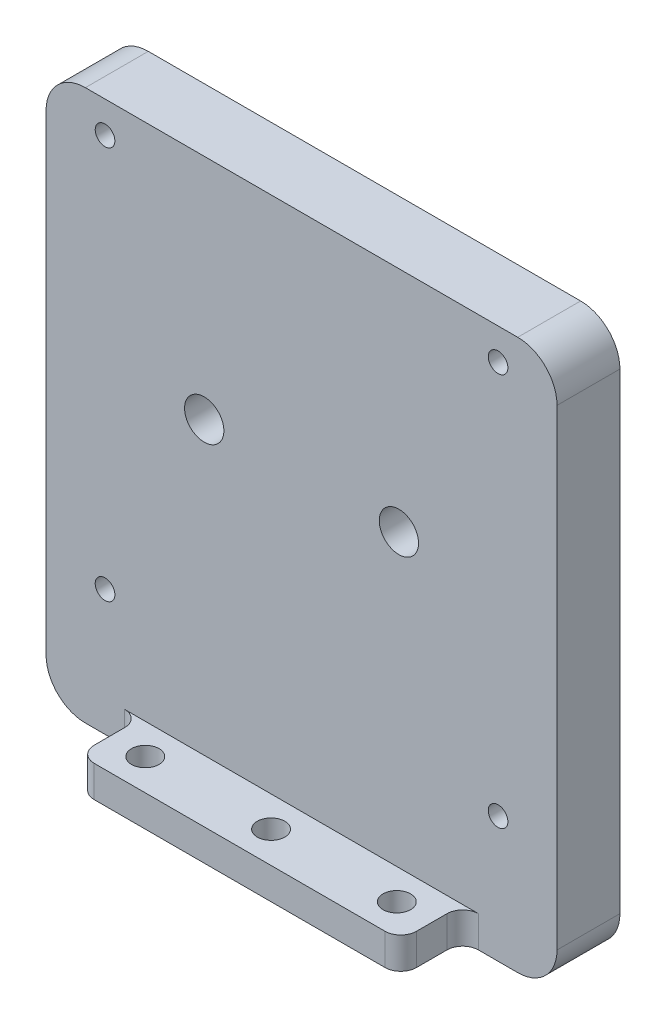
SolidWorks part; units mm, degrees
ref_plane "Front Plane" through (0, 0, 0) normal (0, 0, 1) x (1, 0, 0)
ref_plane "Top Plane" through (0, 0, 0) normal (0, 1, 0) x (1, 0, 0)
ref_plane "Right Plane" through (0, 0, 0) normal (1, 0, 0) x (0, 0, -1)
sketch "Sketch1" plane through (0, 0, 0) normal (0, 0, 1) x (1, 0, 0)
  line L0 (0, 4) -> (0, 0) construction
  line L1 (-32.5, 35) -> (32.5, 35)
  line L2 (-32.5, 35) -> (-32.5, -35)
  line L3 (-32.5, -35) -> (32.5, -35)
  line L4 (32.5, 35) -> (32.5, -35)
  line L5 (-32.5, 35) -> (32.5, -35) construction
  line L6 (-32.5, -35) -> (32.5, 35) construction
  line L7 (25, -21) -> (-25, -21) construction
  line L8 (25, -21) -> (25, 29) construction
  line L9 (25, 29) -> (-25, 29) construction
  line L10 (-25, -21) -> (-25, 29) construction
  line L11 (25, -21) -> (-25, 29) construction
  line L12 (25, 29) -> (-25, -21) construction
  point P0 (0, 0)
  point P6 (0, 4)
  dimension "D1" = 70
  dimension "D2" = 65
  dimension "D4" = 50
  dimension "D5" = 6
extrude "Boss-Extrude1" add sketch "Sketch1" along normal blind 8
fillet "Fillet1" radius 5 4 edges at (32.5, -35, 4) (-32.5, -35, 4) (32.5, 35, 4) (-32.5, 35, 4)
sketch "Sketch2" plane through (0, 0, 8) normal (0, 0, 1) x (1, 0, 0)
  line L0 (-27.5, -35) -> (27.5, -35) construction
  line L1 (-20.5, -35) -> (20.5, -35)
  line L2 (-20.5, -35) -> (-20.5, -31)
  line L3 (-20.5, -31) -> (20.5, -31)
  line L4 (20.5, -35) -> (20.5, -31)
  line L5 (0, 0) -> (0, -31) construction
  dimension "D1" = 41
  dimension "D2" = 4
extrude "Boss-Extrude2" add sketch "Sketch2" along normal blind 7.8799
fillet "Fillet2" radius 2 4 edges at (20.5, -33, 8) (20.5, -33, 15.8799) (-20.5, -33, 15.8799) (-20.5, -33, 8)
sketch "草图1" plane through (0, -35, 0) normal (0, -1, 0) x (1, 0, 0)
  line L0 (-16, 11.8799) -> (0, 11.8799) construction
  line L1 (0, 11.8799) -> (16, 11.8799) construction
  line L2 (-18.5, 15.8799) -> (18.5, 15.8799) construction
  circle A0 centre (-16, 11.8799) radius 1.75
  circle A1 centre (0, 11.8799) radius 1.75
  circle A2 centre (16, 11.8799) radius 1.75
  dimension "D2" = 3.5
  dimension "D1" = 16
  dimension "D3" = 4
extrude "切除-拉伸1" cut sketch "草图1" against normal through all
sketch "草图2" plane through (0, 0, 0) normal (0, 0, -1) x (-1, 0, 0)
  line L0 (-25, 31) -> (25, -19) construction
  line L1 (-25, 31) -> (25, 31) construction
  line L2 (-25, 31) -> (-25, -19) construction
  line L3 (-25, -19) -> (25, -19) construction
  line L4 (25, 31) -> (25, -19) construction
  line L5 (-27.5, 35) -> (27.5, 35) construction
  point P4 (0, 6)
  point P8 (0, 35)
  dimension "D1" = 50
  dimension "D2" = 50
  dimension "D3" = 4
hole_wizard "M3 螺纹孔1" positions "3D草图1" profile "草图3" tap size "M3" standard "ISO"
sketch3d "3D草图1"
  point P0 (25, -19, 0)
  point P3 (25, 31, 0)
  point P6 (-25, 31, 0)
  point P9 (-25, -19, 0)
sketch "草图3" plane through (25, -19, 0) normal (1, 0, 0) x (0, 1, 0)
  line L0 (0, 0) -> (0, 10.7511)
  line L1 (0, 10.7511) -> (1.25, 10)
  line L2 (1.25, 10) -> (1.25, 0)
  line L5 (1.25, 0) -> (0, 0)
  line L10 (0, 10.7511) -> (-1.25, 10) construction
  line L11 (0, -6.35) -> (0, 107.95) construction
  dimension "螺纹孔钻头直径" = 2.5
  dimension "螺纹孔钻头深度" = 10
  dimension "导头角度" = 118
cosmetic thread "孔螺蚊线1" parameters "D1"=6, "D2"=3
cosmetic thread "孔螺蚊线2" parameters "D1"=6, "D2"=3
cosmetic thread "孔螺蚊线3" parameters "D1"=6, "D2"=3
cosmetic thread "孔螺蚊线4" parameters "D1"=6, "D2"=3
ref_plane "基准面1" through (0, 0, -30.31) normal (0, 0, -1) x (-1, 0, 0)
sketch "草图11" plane through (0, 0, -30.31) normal (0, 0, -1) x (-1, 0, 0)
  line L0 (-32.5, 34.15) -> (-32.5, 36.65) construction
  line L1 (32.5, -35) -> (-32.5, -35)
  line L2 (32.5, -35) -> (32.5, 35.4)
  line L3 (32.5, 35.4) -> (-32.5, 35.4)
  line L4 (-32.5, -35) -> (-32.5, 35.4)
extrude "凸台-拉伸1" add sketch "草图11" against normal blind 2.9 separate body
fillet "圆角2" radius 5 1 edges at (-32.5, 35.4, -28.86)
fillet "圆角3" radius 5 1 edges at (-32.5, -35, -28.86)
fillet "圆角4" radius 5 1 edges at (32.5, -35, -28.86)
fillet "圆角5" radius 5 1 edges at (32.5, 35.4, -28.86)
sketch "草图15" plane through (0, 0, -30.31) normal (0, 0, -1) x (-1, 0, 0)
  circle A0 centre (-25, -19) radius 1.7
  circle A1 centre (-25, 31) radius 1.7
  circle A2 centre (25, -19) radius 1.7
  circle A3 centre (25, 31) radius 1.7
hole_wizard "M3 螺纹孔2" positions "草图23" profile "草图24" tap size "M3" standard "ISO" end condition up to next
sketch "草图23" plane through (0, 0, -30.31) normal (0, 0, -1) x (-1, 0, 0)
  point P0 (-25, 31)
  point P3 (25, 31)
  point P6 (-25, -19)
  point P9 (25, -19)
cosmetic thread "孔螺蚊线5" parameters "D2"=3
cosmetic thread "孔螺蚊线6" parameters "D2"=3
cosmetic thread "孔螺蚊线7" parameters "D2"=3
cosmetic thread "孔螺蚊线8" parameters "D2"=3
sketch "草图24" plane through (25, 31, -30.31) normal (1, 0, 0) x (0, 1, 0)
  line L0 (0, 0) -> (0, 2.901)
  line L1 (0, 2.901) -> (1.25, 2.901)
  line L2 (1.25, 2.901) -> (1.25, 0)
  line L5 (1.25, 0) -> (0, 0)
  line L11 (0, -6.35) -> (0, 107.95) construction
  dimension "通孔螺纹孔钻头直径" = 2.5
  dimension "通孔螺纹孔钻头深度" = 2.901
hole_wizard "M4 六角凹头螺钉的柱形沉头孔2" positions "草图26" profile "草图27" counterbore size "M4" standard "ISO" end condition up to next
sketch "草图26" plane through (0, 0, -30.31) normal (0, 0, -1) x (-1, 0, 0)
  point P0 (-9.4177, -9.82)
  point P3 (7.7273, -9.82)
  point P6 (7.7272, 19.876)
  point P9 (-9.4178, 19.876)
sketch "草图27" plane through (9.4177, -9.82, -30.31) normal (1, 0, 0) x (0, 1, 0)
  line L0 (0, 0) -> (0, 38.31)
  line L1 (0, 38.31) -> (2.25, 38.31)
  line L3 (2.25, 38.31) -> (2.25, 1.5)
  line L4 (2.25, 1.5) -> (4, 1.5)
  line L5 (4, 1.5) -> (4, 0)
  line L7 (4, 0) -> (0, 0)
  line L11 (0, -6.35) -> (0, 107.95) construction
  dimension "通孔孔直径" = 4.5
  dimension "通孔孔深度" = 38.31
  dimension "柱形沉头孔直径" = 8
  dimension "柱形沉头孔深度" = 1.5
sketch "草图28" plane through (32.5, 0, 0) normal (1, 0, 0) x (0, 0, -1)
  line L1 (21.2827, 40.5552) -> (37.6286, 40.5552)
  line L2 (21.2827, 40.5552) -> (21.2827, -44.2702)
  line L3 (21.2827, -44.2702) -> (37.6286, -44.2702)
  line L4 (37.6286, 40.5552) -> (37.6286, -44.2702)
extrude "切除-拉伸4" cut sketch "草图28" against normal through all
sketch "草图29" plane through (0, 0, 0) normal (0, 0, -1) x (-1, 0, 0)
  line L0 (-12.3825, 6) -> (12.3825, 6) construction
  line L1 (25, 31) -> (25, -19) construction
  line L2 (-25, -19) -> (25, -19) construction
  point P2 (0, 6)
  point P5 (25, 6)
  point P6 (-8.3163, 6)
  point P9 (0, -19)
  dimension "D1" = 24.765
hole_wizard "M6 螺纹孔1" positions "3D草图2" profile "草图30" tap size "M6" standard "ISO" end condition through all
sketch3d "3D草图2"
  point P0 (12.3825, 6, 0)
  point P3 (-12.3825, 6, 0)
sketch "草图30" plane through (12.3825, 6, 0) normal (1, 0, 0) x (0, 1, 0)
  line L0 (0, 0) -> (0, 15.8799)
  line L1 (0, 15.8799) -> (2.5, 15.8799)
  line L2 (2.5, 15.8799) -> (2.5, 0)
  line L5 (2.5, 0) -> (0, 0)
  line L11 (0, -6.35) -> (0, 107.95) construction
  dimension "通孔螺纹孔钻头直径" = 5
  dimension "通孔螺纹孔钻头深度" = 15.8799
cosmetic thread "孔螺蚊线9" parameters "D2"=6
cosmetic thread "孔螺蚊线10" parameters "D2"=6
